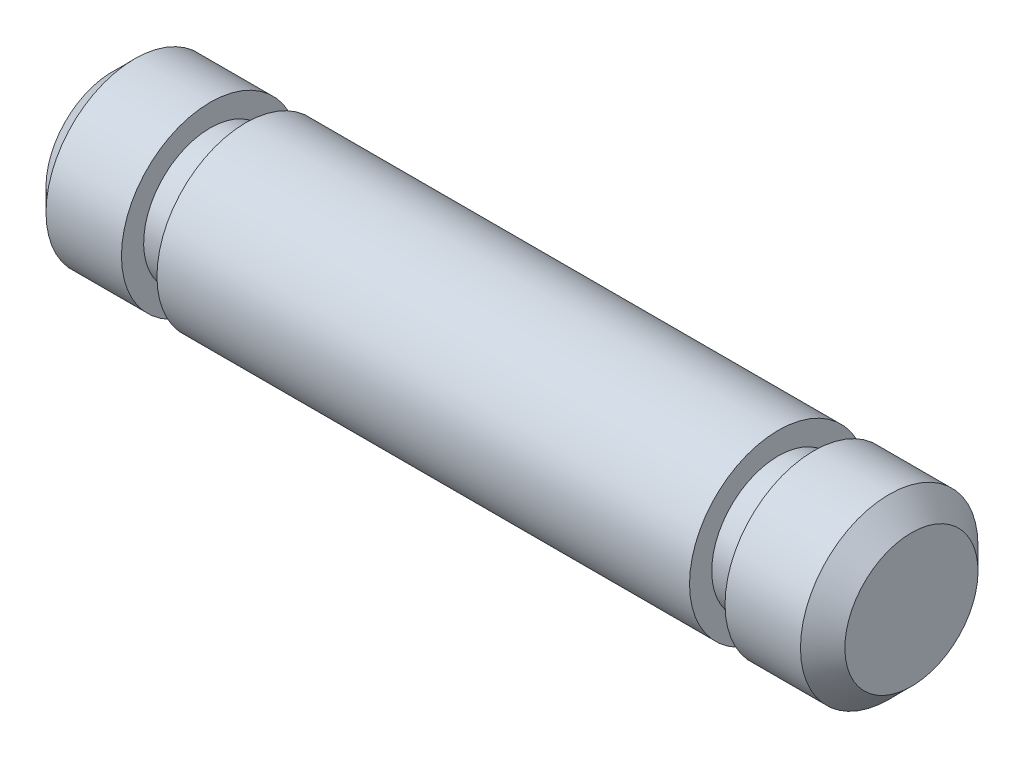
SolidWorks part; units mm, degrees
ref_plane "Front Plane" through (0, 0, 0) normal (0, 0, 1) x (1, 0, 0)
ref_plane "Top Plane" through (0, 0, 0) normal (0, 1, 0) x (1, 0, 0)
ref_plane "Right Plane" through (0, 0, 0) normal (1, 0, 0) x (0, 0, -1)
sketch "Sketch1" plane through (0, 0, 0) normal (0, 0, 1) x (1, 0, 0)
  line L0 (-7.1672, 0) -> (-7.1672, 2)
  line L1 (-7.1672, 2) -> (-4.9672, 2)
  line L2 (-4.9672, 2) -> (-4.9672, 1.5)
  line L3 (-4.9672, 1.5) -> (-4.1672, 1.5)
  line L4 (-4.1672, 1.5) -> (-4.1672, 2)
  line L5 (-4.1672, 2) -> (7.8328, 2)
  line L6 (7.8328, 2) -> (7.8328, 1.5)
  line L7 (7.8328, 1.5) -> (8.6328, 1.5)
  line L8 (8.6328, 1.5) -> (8.6328, 2)
  line L9 (8.6328, 2) -> (10.8328, 2)
  line L10 (10.8328, 2) -> (10.8328, 0)
  line L11 (10.8328, 0) -> (-7.1672, 0)
  point P11 (-7.1672, 1)
  dimension "D1" = 2
  dimension "D2" = 0.8
  dimension "D3" = 0.8
  dimension "D4" = 3
  dimension "D5" = 3
  dimension "D6" = 1.5
  dimension "D7" = 18
revolve "Revolve1" add sketch "Sketch1" angle 360 about L11
chamfer "Chamfer1" distance 0.5 angle 45 2 edges at (10.8328, 2, 0) (-7.1672, 2, 0)
